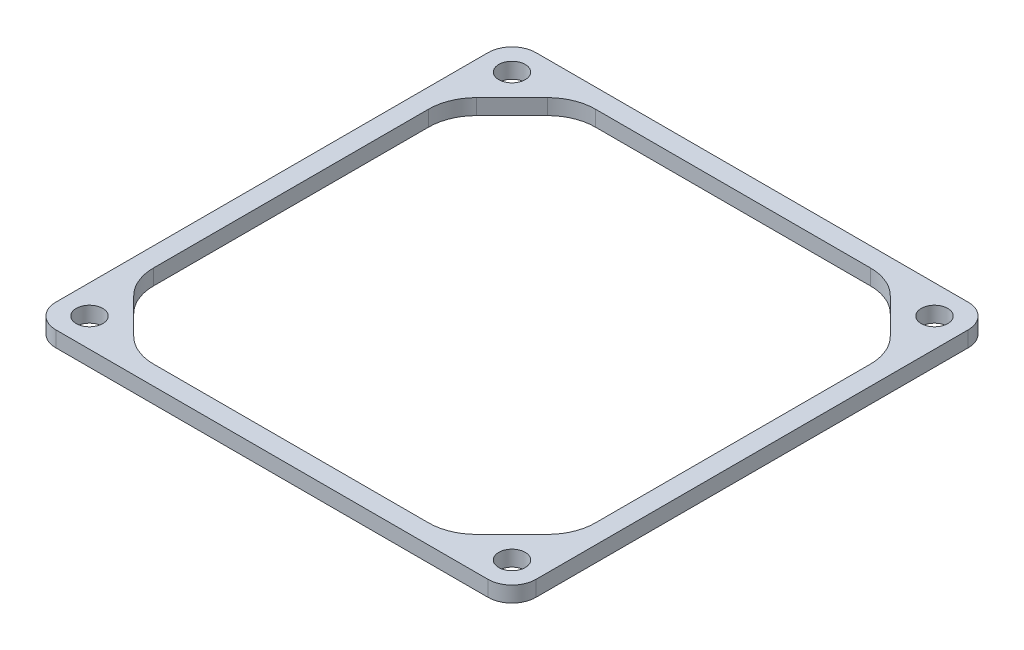
SolidWorks part; units mm, degrees
ref_plane "Front Plane" through (0, 0, 0) normal (0, 0, 1) x (1, 0, 0)
ref_plane "Top Plane" through (0, 0, 0) normal (0, 1, 0) x (1, 0, 0)
ref_plane "Right Plane" through (0, 0, 0) normal (1, 0, 0) x (0, 0, -1)
sketch "Sketch1" plane through (0, 0, 0) normal (0, 1, 0) x (1, 0, 0)
  line L1 (-57.15, 63.5) -> (57.15, 63.5)
  line L2 (-63.5, 57.15) -> (-63.5, -57.15)
  line L3 (-57.15, -63.5) -> (57.15, -63.5)
  line L4 (63.5, 57.15) -> (63.5, -57.15)
  line L5 (-49.403, 53.594) -> (49.403, 53.594) construction
  line L6 (-49.403, 53.594) -> (-49.403, -53.594) construction
  line L7 (-49.403, -53.594) -> (49.403, -53.594) construction
  line L8 (49.403, 53.594) -> (49.403, -53.594) construction
  circle A0 centre (0, 0) radius 44.45
  circle A1 centre (-57.15, 53.975) radius 3.25
  circle A2 centre (57.15, 53.975) radius 3.25
  circle A3 centre (57.15, -53.975) radius 3.25
  circle A4 centre (-57.15, -53.975) radius 3.25
  arc A5 (-63.5, -57.15) -> (-57.15, -63.5) centre (-57.15, -57.15) ccw
  arc A6 (57.15, -63.5) -> (63.5, -57.15) centre (57.15, -57.15) ccw
  arc A7 (57.15, 63.5) -> (63.5, 57.15) centre (57.15, 57.15) cw
  arc A8 (-57.15, 63.5) -> (-63.5, 57.15) centre (-57.15, 57.15) ccw
  point P21 (-63.5, -63.5)
  point P26 (63.5, 63.5)
  point P29 (-63.5, 63.5)
  dimension "D1" = 88.9
  dimension "D10" = 6.5
  dimension "D11" = 6.5
  dimension "D12" = 6.5
  dimension "D13" = 6.5
  dimension "D22" = 6.35
  dimension "D2" = 127
  dimension "D3" = 127
  dimension "D4" = 63.5
  dimension "D5" = 63.5
  dimension "D6" = 107.188
  dimension "D7" = 98.806
  dimension "D8" = 19.812
  dimension "D9" = 14.097
  dimension "D14" = 9.525
  dimension "D15" = 6.35
  dimension "D16" = 9.525
  dimension "D17" = 6.35
  dimension "D18" = 6.35
  dimension "D19" = 9.525
  dimension "D20" = 9.525
  dimension "D21" = 6.35
extrude "Boss-Extrude1" add sketch "Sketch1" along normal blind 3.175
sketch "Sketch3" plane through (0, 3.175, 0) normal (0, 1, 0) x (1, 0, 0)
  line L0 (-54.7003, 45.359) -> (-45.359, 54.7003)
  line L1 (45.359, 54.7003) -> (54.7003, 45.359)
  line L2 (54.7003, -45.359) -> (45.359, -54.7003)
  line L3 (-45.359, -54.7003) -> (-54.7003, -45.359)
  line L4 (-57.15, -63.5) -> (57.15, -63.5)
  line L5 (63.5, -57.15) -> (63.5, 57.15)
  line L6 (57.15, 63.5) -> (-57.15, 63.5)
  line L7 (-63.5, 57.15) -> (-63.5, -57.15)
  line L8 (-57.15, -63.5) -> (57.15, -63.5)
  line L9 (63.5, -57.15) -> (63.5, 57.15)
  line L10 (57.15, 63.5) -> (-57.15, 63.5)
  line L11 (-63.5, 57.15) -> (-63.5, -57.15)
  line L12 (-36.3787, 58.42) -> (36.3787, 58.42)
  line L13 (58.42, -36.3787) -> (58.42, 36.3787)
  line L14 (-36.3787, -58.42) -> (36.3787, -58.42)
  line L15 (-58.42, -36.3787) -> (-58.42, 36.3787)
  arc A0 (36.3787, 58.42) -> (45.359, 54.7003) centre (36.3787, 45.72) cw
  arc A1 (58.42, 36.3787) -> (54.7003, 45.359) centre (45.72, 36.3787) ccw
  arc A2 (58.42, -36.3787) -> (54.7003, -45.359) centre (45.72, -36.3787) cw
  arc A3 (36.3787, -58.42) -> (45.359, -54.7003) centre (36.3787, -45.72) ccw
  arc A4 (-63.5, -57.15) -> (-57.15, -63.5) centre (-57.15, -57.15) ccw
  arc A5 (57.15, -63.5) -> (63.5, -57.15) centre (57.15, -57.15) ccw
  arc A6 (63.5, 57.15) -> (57.15, 63.5) centre (57.15, 57.15) ccw
  arc A7 (-57.15, 63.5) -> (-63.5, 57.15) centre (-57.15, 57.15) ccw
  arc A8 (-63.5, -57.15) -> (-57.15, -63.5) centre (-57.15, -57.15) ccw
  arc A9 (57.15, -63.5) -> (63.5, -57.15) centre (57.15, -57.15) ccw
  arc A10 (63.5, 57.15) -> (57.15, 63.5) centre (57.15, 57.15) ccw
  arc A11 (-57.15, 63.5) -> (-63.5, 57.15) centre (-57.15, 57.15) ccw
  arc A12 (-36.3787, -58.42) -> (-45.359, -54.7003) centre (-36.3787, -45.72) cw
  arc A13 (-58.42, -36.3787) -> (-54.7003, -45.359) centre (-45.72, -36.3787) ccw
  arc A14 (-58.42, 36.3787) -> (-54.7003, 45.359) centre (-45.72, 36.3787) cw
  arc A15 (-36.3787, 58.42) -> (-45.359, 54.7003) centre (-36.3787, 45.72) ccw
  dimension "D2" = 12.7
  dimension "D3" = 72.7574
  dimension "D4" = 72.7574
  dimension "D5" = 72.7574
  dimension "D6" = 72.7574
  dimension "D7" = 135
  dimension "D8" = 135
  dimension "D9" = 135
  dimension "D10" = 135
  dimension "D11" = 180
  dimension "D12" = 180
  dimension "D13" = 180
  dimension "D14" = 13.2106
  dimension "D15" = 13.2106
  dimension "D16" = 8.7997
  dimension "D17" = 11.791
  dimension "D1" = 0
extrude "Boss-Extrude2" add sketch "Sketch3" along normal blind 25.4
hole_wizard "CBORE for M6 SHCS2" positions "Sketch8" profile "Sketch9" counterbore size "M6" standard "ANSI Metric" end condition through all
sketch "Sketch8" plane through (0, 0, 0) normal (0, -1, 0) x (-1, 0, 0)
  line L0 (57.15, -63.5) -> (-57.15, -63.5) construction
  line L1 (63.5, 57.15) -> (63.5, -57.15) construction
  line L2 (-63.5, -57.15) -> (-63.5, 57.15) construction
  line L3 (-57.15, 63.5) -> (57.15, 63.5) construction
  point P0 (-55.88, 55.88)
  point P4 (55.88, 55.88)
  point P6 (55.88, -55.88)
  point P10 (-55.88, -55.88)
  dimension "D1" = 7.62
  dimension "D2" = 7.62
  dimension "D3" = 7.62
  dimension "D4" = 7.62
  dimension "D5" = 7.62
  dimension "D6" = 7.62
  dimension "D7" = 7.62
  dimension "D8" = 7.62
sketch "Sketch9" plane through (55.88, 0, -55.88) normal (1, 0, 0) x (0, 0, -1)
  line L0 (0, 0) -> (0, 28.575)
  line L1 (0, 28.575) -> (3.5, 28.575)
  line L3 (3.5, 28.575) -> (3.5, 6)
  line L4 (3.5, 6) -> (5.5, 6)
  line L5 (5.5, 6) -> (5.5, 0)
  line L7 (5.5, 0) -> (0, 0)
  line L11 (0, -6.35) -> (0, 107.95) construction
  dimension "Thru Hole Dia." = 7
  dimension "Thru Hole Depth" = 28.575
  dimension "C'Bore Dia." = 11
  dimension "C'Bore Depth" = 6
ref_plane "Plane1" through (0, 14.2875, 0) normal (0, -1, 0) x (-1, 0, 0)
sketch "Sketch10" plane through (0, 14.2875, 0) normal (0, -1, 0) x (-1, 0, 0)
  line L1 (-98.5501, 120.0463) -> (107.7253, 120.0463)
  line L2 (-98.5501, 120.0463) -> (-98.5501, -114.3522)
  line L3 (-98.5501, -114.3522) -> (107.7253, -114.3522)
  line L4 (107.7253, 120.0463) -> (107.7253, -114.3522)
extrude "Cut-Extrude1" cut sketch "Sketch10" along normal through all and the other way blind 10.16
hole_wizard "CBORE for M6 SHCS3" positions "Sketch11" profile "Sketch12" counterbore size "M6" standard "ANSI Metric"
sketch "Sketch11" plane through (0, 28.575, 0) normal (0, 1, 0) x (1, 0, 0)
  point P0 (55.88, 55.88)
  point P3 (55.88, -55.88)
  point P6 (-55.88, -55.88)
  point P9 (-55.88, 55.88)
sketch "Sketch12" plane through (55.88, 28.575, -55.88) normal (1, 0, 0) x (0, 0, 1)
  line L0 (0, 0) -> (0, 14.2875)
  line L1 (0, 14.2875) -> (3.5, 14.2875)
  line L3 (3.5, 14.2875) -> (3.5, 8.54)
  line L4 (3.5, 8.54) -> (5.5, 8.54)
  line L5 (5.5, 8.54) -> (5.5, 0)
  line L7 (5.5, 0) -> (0, 0)
  line L11 (0, -6.35) -> (0, 107.95) construction
  dimension "Thru Hole Dia." = 7
  dimension "Thru Hole Depth" = 14.2875
  dimension "C'Bore Dia." = 11
  dimension "C'Bore Depth" = 8.54
equation "\"D4@Sketch1\"=\"D3@Sketch1\"/2"
equation "\"D5@Sketch1\"=\"D2@Sketch1\"/2"
equation "\"D8@Sketch1\"=\"D2@Sketch1\"-\"D6@Sketch1\""
equation "\"D9@Sketch1\"=(\"D3@Sketch1\"-\"D7@Sketch1\")/2"
equation "\"D10@Sketch1\"=6.5/25.4"
equation "\"D11@Sketch1\"=\"D10@Sketch1\""
equation "\"D12@Sketch1\"=\"D10@Sketch1\""
equation "\"D13@Sketch1\"=\"D10@Sketch1\""
